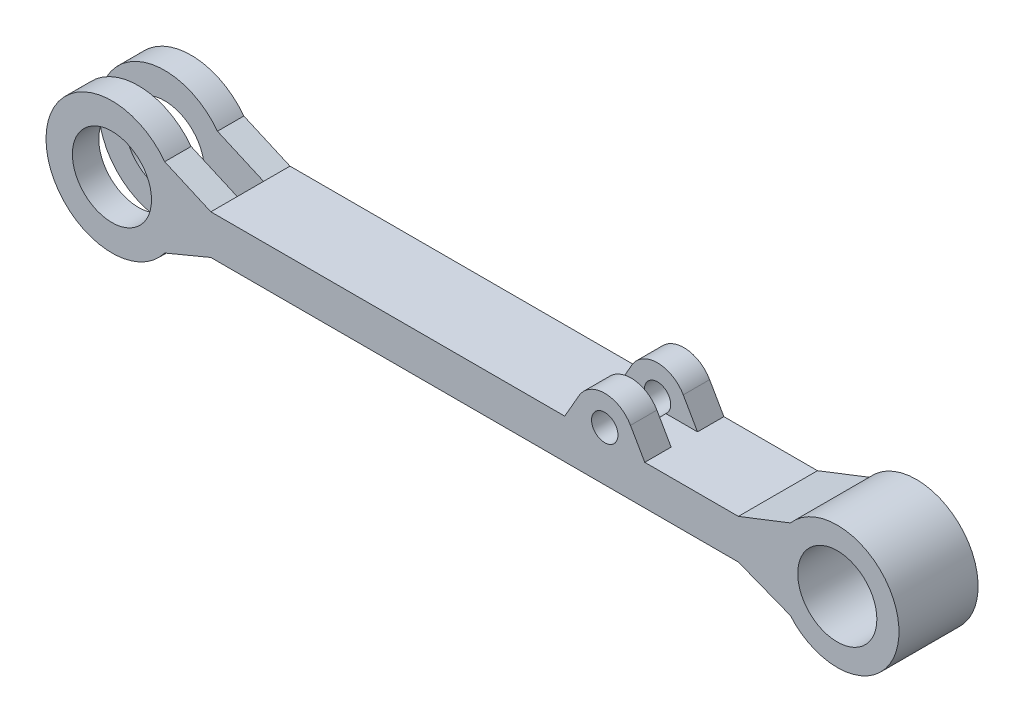
SolidWorks part; units mm, degrees
ref_plane "Front Plane" through (0, 0, 0) normal (0, 0, 1) x (1, 0, 0)
ref_plane "Top Plane" through (0, 0, 0) normal (0, 1, 0) x (1, 0, 0)
ref_plane "Right Plane" through (0, 0, 0) normal (1, 0, 0) x (0, 0, -1)
sketch "Sketch1" plane through (0, 0, 0) normal (0, 0, 1) x (1, 0, 0)
  line L0 (-200, 15) -> (-234.993, 30.4131)
  line L1 (-200, 15) -> (200, 15)
  line L3 (-200, -15) -> (200, -15)
  line L5 (-200, 15) -> (200, -15) construction
  line L6 (-200, -15) -> (200, 15) construction
  line L7 (-200, -15) -> (-234.993, -29.5681)
  line L8 (-234.993, 30.4131) -> (432.8942, 30.4131) construction
  line L9 (-258.7247, -24.779) -> (-258.7247, 25.624) construction
  line L10 (-234.993, -29.5681) -> (354.2169, -29.5681) construction
  line L11 (200, -15) -> (239.4473, -30.4161)
  line L12 (200, 15) -> (239.4473, 30.4161)
  line L13 (0, 0) -> (-200, 0) construction
  line L14 (-200, 15) -> (-200, 0) construction
  line L15 (-200, 0) -> (-200, -15) construction
  circle A0 centre (-275, 0.4225) radius 50
  circle A1 centre (-275, 0.4225) radius 30
  circle A2 centre (275, 0) radius 46.7882
  circle A3 centre (275, 0) radius 30
  point P0 (0, 0)
  point P20 (242.7797, 46.6984)
  point P21 (250.7364, 0)
  point P24 (214.4473, -30.4161)
  point P25 (214.4473, 30.4161)
  point P26 (0, 0)
  point P27 (-209.993, 30.4161)
  point P28 (-209.993, -29.5652)
  dimension "D2" = 100
  dimension "D3" = 75
  dimension "D4" = 75
  dimension "D5" = 15
  dimension "D6" = 60
  dimension "D7" = 60
  dimension "D1" = 400
extrude "Boss-Extrude1" add sketch "Sketch1" along normal blind 60 contours A2 A3 | A2 L12 L1 L0 A0 L7 L3 L11 | A1
sketch "Sketch2" plane through (0, 15, 0) normal (0, 1, 0) x (1, 0, 0)
  line L0 (-325, 0) -> (-200, 0)
  line L1 (-200, 0) -> (-200, -20)
  line L2 (-200, -20) -> (-325, -20)
  line L3 (-325, 0) -> (-325, -60) construction
  line L4 (-325, -20) -> (-325, 0)
  line L5 (-200, -40) -> (-200, -60)
  line L6 (-200, -60) -> (-200, 0) construction
  line L7 (-200, -60) -> (-325, -60)
  line L8 (-325, -60) -> (-325, -40)
  line L9 (-325, -40) -> (-200, -40)
  line L10 (-325, -20) -> (-325, -40)
  line L11 (-200, -20) -> (-200, -40)
  line M4 (-200, 0) -> (-200, -60)
  dimension "D1" = 20
  dimension "D2" = 20
extrude "Cut-Extrude1" cut sketch "Sketch2" against normal mid plane 140 contours L2 L10 L9 M4
sketch "Sketch3" plane through (0, 0, 60) normal (0, 0, 1) x (1, 0, 0)
  line L0 (79.1582, 33.881) -> (68.3418, 15)
  line L1 (-200, 15) -> (200, 15) construction
  line L2 (68.3418, 15) -> (98.6815, 15)
  line L3 (98.6815, 15) -> (129.0213, 15)
  line L4 (129.0213, 15) -> (118.2048, 33.881)
  arc A0 (119.8242, 15) -> (77.5389, 15) centre (98.6815, 22.6966) ccw
  arc A1 (105.066, 15) -> (92.297, 15) centre (98.6815, 22.6966) ccw
  line M4 (200, 15) -> (-200, 15)
  dimension "D1" = 45
extrude "Boss-Extrude2" add sketch "Sketch3" against normal up to surface (60 mm away) contours A1 L3 A0 L2 | A0 L0 L2 | A0 L4 M4 up to face at (305, 0, 0)
sketch "Sketch4" plane through (0, 0, 60) normal (0, 0, 1) x (1, 0, 0)
  circle A0 centre (98.6815, 22.6966) radius 10
extrude "Cut-Extrude2" cut sketch "Sketch4" against normal through all
sketch "Sketch5" plane through (-200, 0, 0) normal (-1, 0, 0) x (0, 0, 1)
  line L0 (20, 15) -> (40, 15)
  line L1 (40, 50.4225) -> (40, -49.5775) construction
  line L2 (40, -15) -> (40, 15) construction
  line L3 (40, 15) -> (40, 45.1966)
  line L4 (60, 45.1966) -> (0, 45.1966) construction
  line L5 (40, 45.1966) -> (20, 45.1966)
  line L6 (20, -49.5775) -> (20, 50.4225) construction
  line L7 (20, 45.1966) -> (20, 15)
extrude "Cut-Extrude3" cut sketch "Sketch5" against normal blind 350
